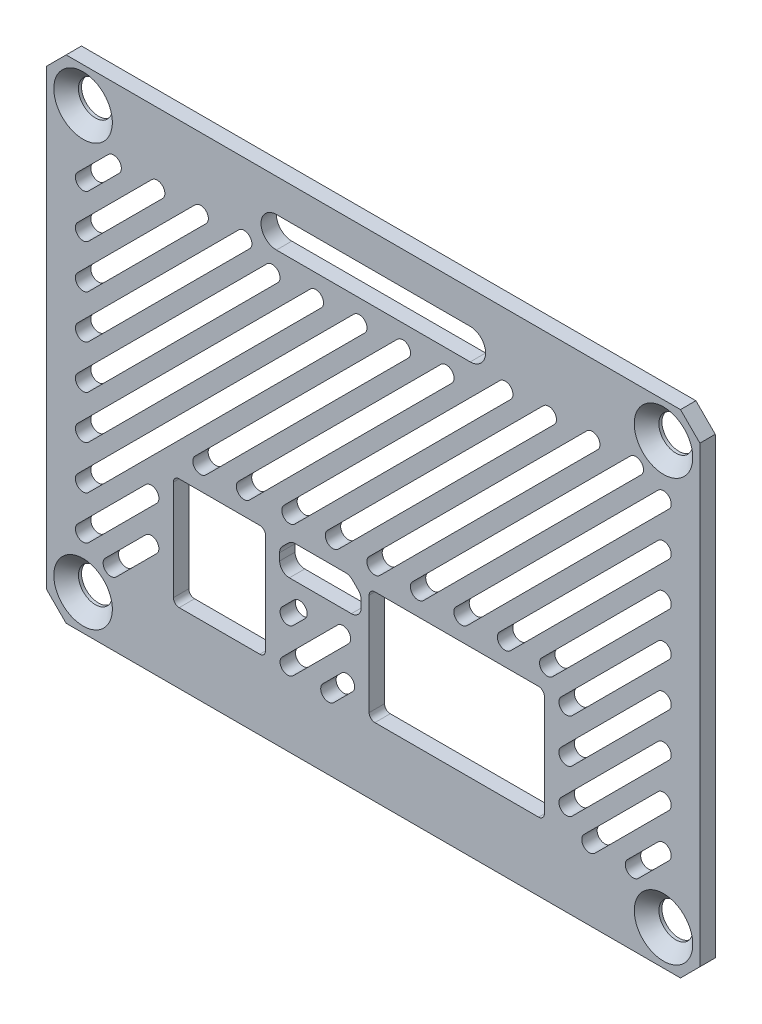
SolidWorks part; units mm, degrees
ref_plane "Front Plane" through (0, 0, 0) normal (0, 0, 1) x (1, 0, 0)
ref_plane "Top Plane" through (0, 0, 0) normal (0, 1, 0) x (1, 0, 0)
ref_plane "Right Plane" through (0, 0, 0) normal (1, 0, 0) x (0, 0, -1)
sketch "Sketch1" plane through (0, 0, 0) normal (0, 0, 1) x (1, 0, 0)
  line L1 (0, 0) -> (67.4, 0)
  line L2 (0, 0) -> (0, 50.8)
  line L3 (0, 50.8) -> (67.4, 50.8)
  line L4 (67.4, 0) -> (67.4, 50.8)
  dimension "D1" = 67.4
  dimension "D2" = 50.8
extrude "Boss-Extrude1" add sketch "Sketch1" along normal blind 1.5875
chamfer "Chamfer1" distance 2 angle 45 4 edges at (0, 0, 0.7937) (67.4, 0, 0.7937) (67.4, 50.8, 0.7937) (0, 50.8, 0.7937)
sketch "Sketch3" plane through (0, 0, 1.5875) normal (0, 0, 1) x (1, 0, 0)
  line L0 (0, 25.4) -> (67.4, 25.4) construction
  line L1 (0, 48.8) -> (0, 2) construction
  line L2 (67.4, 2) -> (67.4, 48.8) construction
  line L3 (3.75, 47.15) -> (63.65, 47.15) construction
  line L4 (65.4, 50.8) -> (2, 50.8) construction
  line L5 (33.7, 50.8) -> (33.7, 0) construction
  line L6 (2, 0) -> (65.4, 0) construction
  line L7 (63.65, 47.15) -> (63.65, 3.65) construction
  circle A0 centre (3.75, 47.15) radius 1.75
  circle A1 centre (3.75, 3.65) radius 1.75
  circle A2 centre (63.65, 3.65) radius 1.75
  circle A3 centre (63.65, 47.15) radius 1.75
  circle A4 centre (63.65, 3.65) radius 1.75 construction
  point P20 (33.7, 47.15)
  point P21 (63.65, 25.4)
  dimension "D1" = 3.5
extrude "Cut-Extrude2" cut sketch "Sketch3" against normal through all
chamfer "Chamfer2" distance 1.27 angle 45 4 edges at (5.5, 3.65, 1.5875) (65.4, 3.65, 1.5875) (65.4, 47.15, 1.5875) (5.5, 47.15, 1.5875)
sketch "Sketch5" plane through (0, 0, 1.5875) normal (0, 0, 1) x (1, 0, 0)
  line L0 (23.7, 45.8) -> (43.7, 45.8) construction
  line L1 (23.7, 47.3875) -> (43.7, 47.3875)
  line L2 (23.7, 44.2125) -> (43.7, 44.2125)
  line L3 (33.7, 50.8) -> (33.7, 45.8) construction
  line L5 (65.4, 50.8) -> (2, 50.8) construction
  arc A0 (23.7, 47.3875) -> (23.7, 44.2125) centre (23.7, 45.8) ccw
  arc A1 (43.7, 44.2125) -> (43.7, 47.3875) centre (43.7, 45.8) ccw
  point P2 (33.7, 45.8)
  dimension "D2" = 1.5875
  dimension "D1" = 20
  dimension "D3" = 5
extrude "Cut-Extrude4" cut sketch "Sketch5" against normal through all
sketch "Sketch2" plane through (0, 0, 1.5875) normal (0, 0, 1) x (1, 0, 0)
  line L0 (33.5222, 7.3115) -> (51.099, 7.3115) construction
  line L1 (50.7577, 7.0575) -> (33.8635, 7.0575)
  line L2 (51.353, 7.6528) -> (51.353, 18.1462)
  line L3 (50.7577, 18.7415) -> (33.8635, 18.7415)
  line L4 (33.2682, 7.6528) -> (33.2682, 18.1462)
  line L5 (21.9838, 7.2335) -> (13.6664, 7.2335)
  line L6 (22.5791, 7.8288) -> (22.5791, 18.1462)
  line L7 (21.9838, 18.7415) -> (13.6664, 18.7415)
  line L8 (13.0711, 7.8288) -> (13.0711, 18.1462)
  line L9 (51.099, 7.3115) -> (51.099, 18.4875) construction
  line L10 (33.5222, 18.4875) -> (33.5222, 7.3115) construction
  line L12 (13.3251, 7.4875) -> (22.3251, 7.4875) construction
  line L13 (13.3251, 7.4875) -> (13.3251, 18.4875) construction
  line L14 (22.3251, 18.4875) -> (22.3251, 7.4875) construction
  line L15 (22.3251, 18.4875) -> (13.3251, 18.4875) construction
  line L16 (24.0349, 17.3339) -> (24.0349, 16.5875)
  line L17 (28.2389, 15.8375) -> (28.2389, 18.6875) construction
  line L18 (24.2889, 17.3339) -> (24.2889, 16.5875) construction
  line L19 (25.1122, 18.4678) -> (24.5086, 17.8643) construction
  line L20 (31.4389, 15.5835) -> (25.0389, 15.5835)
  line L21 (32.4429, 17.3339) -> (32.4429, 16.5875)
  line L22 (31.5453, 18.6474) -> (32.1489, 18.0439)
  line L23 (25.6425, 18.9415) -> (30.8354, 18.9415)
  line L24 (24.9326, 18.6474) -> (24.329, 18.0439)
  line L25 (51.099, 18.4875) -> (33.5222, 18.4875) construction
  line L62 (25.6425, 18.6875) -> (30.8354, 18.6875) construction
  line L67 (31.4389, 15.8375) -> (25.0389, 15.8375) construction
  line L70 (31.3657, 18.4678) -> (31.9693, 17.8643) construction
  line L73 (32.1889, 17.3339) -> (32.1889, 16.5875) construction
  arc A0 (25.0389, 15.8375) -> (24.2889, 16.5875) centre (25.0389, 16.5875) cw construction
  arc A1 (24.2889, 17.3339) -> (24.5086, 17.8643) centre (25.0389, 17.3339) cw construction
  arc A2 (25.1122, 18.4678) -> (25.6425, 18.6875) centre (25.6425, 17.9375) cw construction
  arc A3 (31.4389, 16.0375) -> (31.9889, 16.5875) centre (31.4389, 16.5875) ccw construction
  arc A4 (13.6664, 18.7415) -> (13.0711, 18.1462) centre (13.6664, 18.1462) ccw
  arc A5 (13.0711, 7.8288) -> (13.6664, 7.2335) centre (13.6664, 7.8288) ccw
  arc A6 (22.5791, 7.8288) -> (21.9838, 7.2335) centre (21.9838, 7.8288) cw
  arc A7 (21.9838, 18.7415) -> (22.5791, 18.1462) centre (21.9838, 18.1462) cw
  arc A8 (33.2682, 18.1462) -> (33.8635, 18.7415) centre (33.8635, 18.1462) cw
  arc A9 (50.7577, 18.7415) -> (51.353, 18.1462) centre (50.7577, 18.1462) cw
  arc A10 (33.8635, 7.0575) -> (33.2682, 7.6528) centre (33.8635, 7.6528) cw
  arc A11 (50.7577, 7.0575) -> (51.353, 7.6528) centre (50.7577, 7.6528) ccw
  arc A12 (25.0389, 15.5835) -> (24.0349, 16.5875) centre (25.0389, 16.5875) cw
  arc A13 (31.4389, 15.5835) -> (32.4429, 16.5875) centre (31.4389, 16.5875) ccw
  arc A14 (32.4429, 17.3339) -> (32.1489, 18.0439) centre (31.4389, 17.3339) ccw
  arc A15 (31.5453, 18.6474) -> (30.8354, 18.9415) centre (30.8354, 17.9375) ccw
  arc A16 (24.9326, 18.6474) -> (25.6425, 18.9415) centre (25.6425, 17.9375) cw
  arc A17 (24.0349, 17.3339) -> (24.329, 18.0439) centre (25.0389, 17.3339) cw
  arc A27 (31.3657, 18.4678) -> (30.8354, 18.6875) centre (30.8354, 17.9375) ccw construction
  arc A28 (32.1889, 17.3339) -> (31.9693, 17.8643) centre (31.4389, 17.3339) ccw construction
  arc A29 (31.4389, 15.8375) -> (32.1889, 16.5875) centre (31.4389, 16.5875) ccw construction
  dimension "D11" = 0.75
  dimension "D12" = 135
  dimension "D14" = 0.5953
  dimension "D1" = 0.254
  dimension "D2" = 0.254
  dimension "D3" = 0.254
  dimension "D4" = 0.254
  dimension "D5" = 0.254
  dimension "D6" = 0.254
  dimension "D7" = 0.254
  dimension "D8" = 0.254
  dimension "D9" = 2.85
  dimension "D10" = 3.95
  dimension "D13" = 2.5964
extrude "Cut-Extrude1" cut sketch "Sketch2" against normal through all
sketch "Sketch6" plane through (0, 0, 1.5875) normal (0, 0, 1) x (1, 0, 0)
  line L0 (60.8864, 6.5) -> (6.5136, 6.5) construction
  line L1 (64.4437, 6.5) -> (2.9562, 6.5) construction
  line L2 (64.4437, 6.5) -> (64.4437, 44.3) construction
  line L3 (64.4437, 44.3) -> (2.9562, 44.3) construction
  line L4 (2.9562, 6.5) -> (2.9562, 44.3) construction
  line L5 (6.5136, 44.3) -> (16.75, 44.3) construction
  line L6 (64.4437, 6.5) -> (64.4437, 44.3) construction
  line L7 (2.9562, 6.5) -> (2.9562, 44.3) construction
  line L8 (63.65, 10.4487) -> (60.495, 7.2937) construction
  line L9 (64.2113, 9.8875) -> (61.0563, 6.7325)
  line L10 (63.0887, 11.01) -> (59.9338, 7.855)
  line L11 (63.65, 14.9388) -> (56.0049, 7.2937) construction
  line L12 (64.2113, 14.3776) -> (56.5662, 6.7325)
  line L13 (63.0887, 15.5001) -> (55.4436, 7.855)
  line L14 (63.65, 19.429) -> (53.6467, 9.4257) construction
  line L15 (64.2113, 18.8677) -> (54.208, 8.8645)
  line L16 (63.0887, 19.9902) -> (53.0855, 9.987)
  line L17 (63.65, 23.9191) -> (53.6467, 13.9159) construction
  line L18 (64.2113, 23.3578) -> (54.208, 13.3546)
  line L19 (63.0887, 24.4804) -> (53.0855, 14.4771)
  line L20 (63.65, 28.4092) -> (53.6467, 18.406) construction
  line L21 (64.2113, 27.848) -> (54.208, 17.8447)
  line L22 (63.0887, 28.9705) -> (53.0855, 18.9672)
  line L23 (63.65, 10.4487) -> (61.4049, 12.6938) construction
  line L24 (63.65, 18.4) -> (63.65, 16.9) construction
  line L25 (63.65, 14.9388) -> (61.4049, 17.1839) construction
  line L26 (6.905, 43.5063) -> (3.75, 40.3513) construction
  line L27 (7.4662, 42.945) -> (4.3113, 39.79)
  line L28 (6.3437, 44.0675) -> (3.1887, 40.9125)
  line L29 (9.15, 41.2612) -> (6.905, 43.5063) construction
  line L30 (63.65, 19.429) -> (61.4049, 21.674) construction
  line L31 (5.3275, 41.9288) -> (2.9562, 44.3) construction
  line L32 (63.65, 23.9191) -> (61.4049, 26.1642) construction
  line L33 (63.65, 32.8994) -> (51.6459, 20.8953) construction
  line L34 (50.7577, 20.2415) -> (33.8635, 20.2415)
  line L35 (31.7682, 18.1462) -> (31.7682, 7.6528)
  line L36 (33.8635, 5.5575) -> (50.7577, 5.5575)
  line L37 (52.853, 7.6528) -> (52.853, 18.1462)
  line L38 (50.7577, 20.2415) -> (33.8635, 20.2415) construction
  line L39 (31.7682, 18.1462) -> (31.7682, 7.6528) construction
  line L40 (33.8635, 5.5575) -> (50.7577, 5.5575) construction
  line L41 (52.853, 7.6528) -> (52.853, 18.1462) construction
  line L42 (64.2113, 32.3381) -> (52.2072, 20.334)
  line L43 (63.0887, 33.4606) -> (51.0847, 21.4566)
  line L44 (63.65, 28.4092) -> (61.4049, 30.6543) construction
  line L45 (63.65, 37.3895) -> (47.2958, 21.0353) construction
  line L46 (64.2113, 36.8282) -> (47.857, 20.474)
  line L47 (63.0887, 37.9508) -> (46.7345, 21.5965)
  line L48 (63.65, 32.8994) -> (61.4049, 35.1444) construction
  line L49 (63.65, 41.8796) -> (42.8056, 21.0353) construction
  line L50 (64.2113, 41.3183) -> (43.3669, 20.474)
  line L51 (63.0887, 42.4409) -> (42.2444, 21.5965)
  line L52 (63.65, 37.3895) -> (61.4049, 39.6346) construction
  line L53 (60.7865, 43.5063) -> (38.3155, 21.0353) construction
  line L54 (61.3478, 42.945) -> (38.8768, 20.474)
  line L55 (60.2252, 44.0675) -> (37.7542, 21.5965)
  line L56 (63.0316, 41.2612) -> (60.7865, 43.5063) construction
  line L57 (62.0725, 8.8712) -> (64.4437, 6.5) construction
  line L58 (26.0799, 13.2897) -> (24.8729, 12.0827) construction
  line L59 (26.6411, 12.7285) -> (25.4341, 11.5215)
  line L60 (25.5186, 13.851) -> (24.3116, 12.644)
  line L61 (30.57, 13.2897) -> (24.8729, 7.5926) construction
  line L62 (56.2964, 43.5063) -> (33.8254, 21.0353) construction
  line L63 (56.8576, 42.945) -> (34.3866, 20.474)
  line L64 (23.8719, 19.7081) -> (23.2683, 19.1045)
  line L65 (22.5349, 17.3339) -> (22.5349, 16.5875)
  line L66 (25.0389, 14.0835) -> (31.4389, 14.0835)
  line L67 (33.9429, 16.5875) -> (33.9429, 17.3339)
  line L68 (33.2095, 19.1045) -> (32.606, 19.7081)
  line L69 (30.8354, 20.4415) -> (25.6425, 20.4415)
  line L70 (23.8719, 19.7081) -> (23.2683, 19.1045) construction
  line L71 (22.5349, 17.3339) -> (22.5349, 16.5875) construction
  line L72 (25.0389, 14.0835) -> (31.4389, 14.0835) construction
  line L73 (33.9429, 16.5875) -> (33.9429, 17.3339) construction
  line L74 (33.2095, 19.1045) -> (32.606, 19.7081) construction
  line L75 (30.8354, 20.4415) -> (25.6425, 20.4415) construction
  line L76 (55.7351, 44.0675) -> (33.2641, 21.5965)
  line L77 (58.5414, 41.2612) -> (56.2964, 43.5063) construction
  line L78 (21.9838, 20.2415) -> (13.6664, 20.2415)
  line L79 (11.5711, 18.1462) -> (11.5711, 7.8288)
  line L80 (13.6664, 5.7335) -> (21.9838, 5.7335)
  line L81 (24.0791, 7.8288) -> (24.0791, 18.1462)
  line L82 (21.9838, 20.2415) -> (13.6664, 20.2415) construction
  line L83 (11.5711, 18.1462) -> (11.5711, 7.8288) construction
  line L84 (13.6664, 5.7335) -> (21.9838, 5.7335) construction
  line L85 (24.0791, 7.8288) -> (24.0791, 18.1462) construction
  line L86 (51.8063, 43.5063) -> (29.5352, 21.2352) construction
  line L87 (52.3675, 42.945) -> (30.0965, 20.674)
  line L88 (51.245, 44.0675) -> (28.974, 21.7965)
  line L89 (54.0513, 41.2612) -> (51.8063, 43.5063) construction
  line L90 (47.3161, 43.5063) -> (25.0451, 21.2352) construction
  line L91 (47.8774, 42.945) -> (25.6064, 20.674)
  line L92 (46.7549, 44.0675) -> (24.4839, 21.7965)
  line L93 (49.5612, 41.2612) -> (47.3161, 43.5063) construction
  line L94 (41.2385, 41.9188) -> (20.355, 21.0352) construction
  line L95 (41.7998, 41.3575) -> (20.9163, 20.474)
  line L96 (40.6772, 42.48) -> (19.7937, 21.5965)
  line L97 (43.4836, 39.6737) -> (41.2385, 41.9188) construction
  line L98 (36.7484, 41.9188) -> (15.8649, 21.0352) construction
  line L99 (37.3096, 41.3575) -> (16.4261, 20.474)
  line L100 (36.1871, 42.48) -> (15.3036, 21.5965)
  line L101 (38.9934, 39.6737) -> (36.7484, 41.9188) construction
  line L102 (32.2582, 41.9188) -> (3.75, 13.4105) construction
  line L103 (32.8195, 41.3575) -> (4.3113, 12.8492)
  line L104 (31.697, 42.48) -> (3.1887, 13.9718)
  line L105 (34.5033, 39.6737) -> (32.2582, 41.9188) construction
  line L106 (31.1313, 12.7285) -> (25.4341, 7.0313)
  line L107 (30.0087, 13.851) -> (24.3116, 8.1539)
  line L108 (27.7681, 41.9188) -> (3.75, 17.9006) construction
  line L109 (28.3294, 41.3575) -> (4.3113, 17.3394)
  line L110 (43.7, 48.8875) -> (23.7, 48.8875)
  line L111 (23.7, 42.7125) -> (43.7, 42.7125)
  line L112 (43.7, 48.8875) -> (23.7, 48.8875) construction
  line L113 (23.7, 42.7125) -> (43.7, 42.7125) construction
  line L114 (27.2068, 42.48) -> (3.1887, 18.4619)
  line L115 (30.0132, 39.6737) -> (27.7681, 41.9188) construction
  line L116 (23.278, 41.9188) -> (3.75, 22.3908) construction
  line L117 (23.8392, 41.3575) -> (4.3113, 21.8295)
  line L118 (22.7167, 42.48) -> (3.1887, 22.952)
  line L119 (25.523, 39.6737) -> (23.278, 41.9188) construction
  line L120 (20.3754, 43.5063) -> (3.75, 26.8809) construction
  line L121 (20.9366, 42.945) -> (4.3113, 26.3196)
  line L122 (19.8141, 44.0675) -> (3.1887, 27.4422)
  line L123 (22.6204, 41.2612) -> (20.3754, 43.5063) construction
  line L124 (15.8852, 43.5063) -> (3.75, 31.371) construction
  line L125 (16.4465, 42.945) -> (4.3113, 30.8098)
  line L126 (15.324, 44.0675) -> (3.1887, 31.9323)
  line L127 (18.1303, 41.2612) -> (15.8852, 43.5063) construction
  line L128 (11.3951, 43.5063) -> (3.75, 35.8612) construction
  line L129 (11.9564, 42.945) -> (4.3113, 35.2999)
  line L130 (10.8338, 44.0675) -> (3.1887, 36.4224)
  line L131 (13.6402, 41.2612) -> (11.3951, 43.5063) construction
  line L132 (30.9745, 9.2041) -> (29.0641, 7.2937) construction
  line L133 (31.5357, 8.6428) -> (29.6254, 6.7325)
  line L134 (30.4132, 9.7653) -> (28.5029, 7.855)
  line L135 (10.7774, 15.9478) -> (3.75, 8.9204) construction
  line L136 (11.3386, 15.3865) -> (4.3113, 8.3591)
  line L137 (10.2161, 16.509) -> (3.1887, 9.4817)
  line L138 (10.7774, 11.4576) -> (6.6135, 7.2937) construction
  line L139 (11.3386, 10.8964) -> (7.1748, 6.7325)
  line L140 (10.2161, 12.0189) -> (6.0522, 7.855)
  arc A0 (64.2113, 9.8875) -> (63.0887, 11.01) centre (63.65, 10.4487) ccw
  arc A1 (59.9338, 7.855) -> (61.0563, 6.7325) centre (60.495, 7.2937) ccw
  arc A2 (64.2113, 14.3776) -> (63.0887, 15.5001) centre (63.65, 14.9388) ccw
  arc A3 (55.4436, 7.855) -> (56.5662, 6.7325) centre (56.0049, 7.2937) ccw
  arc A4 (64.2113, 18.8677) -> (63.0887, 19.9902) centre (63.65, 19.429) ccw
  arc A5 (53.0855, 9.987) -> (54.208, 8.8645) centre (53.6467, 9.4257) ccw
  arc A6 (64.2113, 23.3578) -> (63.0887, 24.4804) centre (63.65, 23.9191) ccw
  arc A7 (53.0855, 14.4771) -> (54.208, 13.3546) centre (53.6467, 13.9159) ccw
  arc A8 (64.2113, 27.848) -> (63.0887, 28.9705) centre (63.65, 28.4092) ccw
  arc A9 (53.0855, 18.9672) -> (54.208, 17.8447) centre (53.6467, 18.406) ccw
  arc A10 (7.4662, 42.945) -> (6.3437, 44.0675) centre (6.905, 43.5063) ccw
  arc A11 (3.1887, 40.9125) -> (4.3113, 39.79) centre (3.75, 40.3513) ccw
  arc A12 (26.6411, 12.7285) -> (25.5186, 13.851) centre (26.0799, 13.2897) ccw
  arc A13 (24.3116, 12.644) -> (25.4341, 11.5215) centre (24.8729, 12.0827) ccw
  arc A14 (64.2113, 32.3381) -> (63.0887, 33.4606) centre (63.65, 32.8994) ccw
  arc A15 (51.0847, 21.4566) -> (52.2072, 20.334) centre (51.6459, 20.8953) ccw
  arc A16 (64.2113, 36.8282) -> (63.0887, 37.9508) centre (63.65, 37.3895) ccw
  arc A17 (46.7345, 21.5965) -> (47.857, 20.474) centre (47.2958, 21.0353) ccw
  arc A18 (52.853, 18.1462) -> (50.7577, 20.2415) centre (50.7577, 18.1462) ccw
  arc A19 (33.8635, 20.2415) -> (31.7682, 18.1462) centre (33.8635, 18.1462) ccw
  arc A20 (31.7682, 7.6528) -> (33.8635, 5.5575) centre (33.8635, 7.6528) ccw
  arc A21 (50.7577, 5.5575) -> (52.853, 7.6528) centre (50.7577, 7.6528) ccw
  arc A22 (52.853, 18.1462) -> (50.7577, 20.2415) centre (50.7577, 18.1462) ccw construction
  arc A23 (33.8635, 20.2415) -> (31.7682, 18.1462) centre (33.8635, 18.1462) ccw construction
  arc A24 (31.7682, 7.6528) -> (33.8635, 5.5575) centre (33.8635, 7.6528) ccw construction
  arc A25 (50.7577, 5.5575) -> (52.853, 7.6528) centre (50.7577, 7.6528) ccw construction
  arc A26 (64.2113, 41.3183) -> (63.0887, 42.4409) centre (63.65, 41.8796) ccw
  arc A27 (42.2444, 21.5965) -> (43.3669, 20.474) centre (42.8056, 21.0353) ccw
  arc A28 (61.3478, 42.945) -> (60.2252, 44.0675) centre (60.7865, 43.5063) ccw
  arc A29 (37.7542, 21.5965) -> (38.8768, 20.474) centre (38.3155, 21.0353) ccw
  arc A30 (31.1313, 12.7285) -> (30.0087, 13.851) centre (30.57, 13.2897) ccw
  arc A31 (24.3116, 8.1539) -> (25.4341, 7.0313) centre (24.8729, 7.5926) ccw
  arc A32 (31.5357, 8.6428) -> (30.4132, 9.7653) centre (30.9745, 9.2041) ccw
  arc A33 (28.5029, 7.855) -> (29.6254, 6.7325) centre (29.0641, 7.2937) ccw
  arc A34 (11.3386, 15.3865) -> (10.2161, 16.509) centre (10.7774, 15.9478) ccw
  arc A35 (3.1887, 9.4817) -> (4.3113, 8.3591) centre (3.75, 8.9204) ccw
  arc A36 (56.8576, 42.945) -> (55.7351, 44.0675) centre (56.2964, 43.5063) ccw
  arc A37 (33.2641, 21.5965) -> (34.3866, 20.474) centre (33.8254, 21.0353) ccw
  arc A38 (25.6425, 20.4415) -> (23.8719, 19.7081) centre (25.6425, 17.9375) ccw
  arc A39 (23.2683, 19.1045) -> (22.5349, 17.3339) centre (25.0389, 17.3339) ccw
  arc A40 (22.5349, 16.5875) -> (25.0389, 14.0835) centre (25.0389, 16.5875) ccw
  arc A41 (31.4389, 14.0835) -> (33.9429, 16.5875) centre (31.4389, 16.5875) ccw
  arc A42 (33.9429, 17.3339) -> (33.2095, 19.1045) centre (31.4389, 17.3339) ccw
  arc A43 (32.606, 19.7081) -> (30.8354, 20.4415) centre (30.8354, 17.9375) ccw
  arc A44 (25.6425, 20.4415) -> (23.8719, 19.7081) centre (25.6425, 17.9375) ccw construction
  arc A45 (23.2683, 19.1045) -> (22.5349, 17.3339) centre (25.0389, 17.3339) ccw construction
  arc A46 (22.5349, 16.5875) -> (25.0389, 14.0835) centre (25.0389, 16.5875) ccw construction
  arc A47 (31.4389, 14.0835) -> (33.9429, 16.5875) centre (31.4389, 16.5875) ccw construction
  arc A48 (33.9429, 17.3339) -> (33.2095, 19.1045) centre (31.4389, 17.3339) ccw construction
  arc A49 (32.606, 19.7081) -> (30.8354, 20.4415) centre (30.8354, 17.9375) ccw construction
  arc A50 (52.3675, 42.945) -> (51.245, 44.0675) centre (51.8063, 43.5063) ccw
  arc A51 (28.974, 21.7965) -> (30.0965, 20.674) centre (29.5352, 21.2352) ccw
  arc A52 (24.0791, 18.1462) -> (21.9838, 20.2415) centre (21.9838, 18.1462) ccw
  arc A53 (13.6664, 20.2415) -> (11.5711, 18.1462) centre (13.6664, 18.1462) ccw
  arc A54 (11.5711, 7.8288) -> (13.6664, 5.7335) centre (13.6664, 7.8288) ccw
  arc A55 (21.9838, 5.7335) -> (24.0791, 7.8288) centre (21.9838, 7.8288) ccw
  arc A56 (24.0791, 18.1462) -> (21.9838, 20.2415) centre (21.9838, 18.1462) ccw construction
  arc A57 (13.6664, 20.2415) -> (11.5711, 18.1462) centre (13.6664, 18.1462) ccw construction
  arc A58 (11.5711, 7.8288) -> (13.6664, 5.7335) centre (13.6664, 7.8288) ccw construction
  arc A59 (21.9838, 5.7335) -> (24.0791, 7.8288) centre (21.9838, 7.8288) ccw construction
  arc A60 (47.8774, 42.945) -> (46.7549, 44.0675) centre (47.3161, 43.5063) ccw
  arc A61 (24.4839, 21.7965) -> (25.6064, 20.674) centre (25.0451, 21.2352) ccw
  arc A62 (41.7998, 41.3575) -> (40.6772, 42.48) centre (41.2385, 41.9188) ccw
  arc A63 (19.7937, 21.5965) -> (20.9163, 20.474) centre (20.355, 21.0352) ccw
  arc A64 (37.3096, 41.3575) -> (36.1871, 42.48) centre (36.7484, 41.9188) ccw
  arc A65 (15.3036, 21.5965) -> (16.4261, 20.474) centre (15.8649, 21.0352) ccw
  arc A66 (32.8195, 41.3575) -> (31.697, 42.48) centre (32.2582, 41.9188) ccw
  arc A67 (3.1887, 13.9718) -> (4.3113, 12.8492) centre (3.75, 13.4105) ccw
  arc A68 (11.3386, 10.8964) -> (10.2161, 12.0189) centre (10.7774, 11.4576) ccw
  arc A69 (6.0522, 7.855) -> (7.1748, 6.7325) centre (6.6135, 7.2937) ccw
  arc A70 (28.3294, 41.3575) -> (27.2068, 42.48) centre (27.7681, 41.9188) ccw
  arc A71 (3.1887, 18.4619) -> (4.3113, 17.3394) centre (3.75, 17.9006) ccw
  arc A72 (23.7, 48.8875) -> (23.7, 42.7125) centre (23.7, 45.8) ccw
  arc A73 (43.7, 42.7125) -> (43.7, 48.8875) centre (43.7, 45.8) ccw
  arc A74 (23.7, 48.8875) -> (23.7, 42.7125) centre (23.7, 45.8) ccw construction
  arc A75 (43.7, 42.7125) -> (43.7, 48.8875) centre (43.7, 45.8) ccw construction
  arc A76 (23.8392, 41.3575) -> (22.7167, 42.48) centre (23.278, 41.9188) ccw
  arc A77 (3.1887, 22.952) -> (4.3113, 21.8295) centre (3.75, 22.3908) ccw
  arc A78 (20.9366, 42.945) -> (19.8141, 44.0675) centre (20.3754, 43.5063) ccw
  arc A79 (3.1887, 27.4422) -> (4.3113, 26.3196) centre (3.75, 26.8809) ccw
  arc A80 (16.4465, 42.945) -> (15.324, 44.0675) centre (15.8852, 43.5063) ccw
  arc A81 (3.1887, 31.9323) -> (4.3113, 30.8098) centre (3.75, 31.371) ccw
  arc A82 (11.9564, 42.945) -> (10.8338, 44.0675) centre (11.3951, 43.5063) ccw
  arc A83 (3.1887, 36.4224) -> (4.3113, 35.2999) centre (3.75, 35.8612) ccw
  point P14 (62.0725, 8.8712)
  point P21 (59.8275, 11.1163)
  point P26 (58.6484, 14.4274)
  point P33 (58.6484, 18.9175)
  point P40 (58.6484, 23.4076)
  point P57 (57.648, 26.8973)
  point P78 (55.4729, 29.2124)
  point P87 (53.2278, 31.4574)
  point P96 (49.551, 32.2708)
  point P105 (45.0609, 32.2708)
  point P114 (40.6707, 32.3708)
  point P153 (36.1806, 32.3708)
  point P162 (30.7967, 31.477)
  point P171 (26.3066, 31.477)
  point P180 (18.0041, 27.6646)
  point P189 (15.7591, 29.9097)
  point P204 (13.514, 32.1548)
  point P213 (12.0627, 35.1936)
  point P222 (9.8176, 37.4386)
  point P231 (7.5725, 39.6837)
  point P240 (5.3275, 41.9288)
  point P253 (25.4764, 12.6862)
  point P258 (27.7214, 10.4412)
  point P265 (30.0193, 8.2489)
  point P272 (7.2637, 12.4341)
  point P279 (8.6954, 9.3757)
  dimension "D2" = 0.7937
  dimension "D1" = 45
  dimension "D4" = 3.175
  dimension "D5" = 1.5
  dimension "D6" = 1.5
  dimension "D7" = 1.5
  dimension "D8" = 1.5
extrude "Cut-Extrude5" cut sketch "Sketch6" against normal through all
